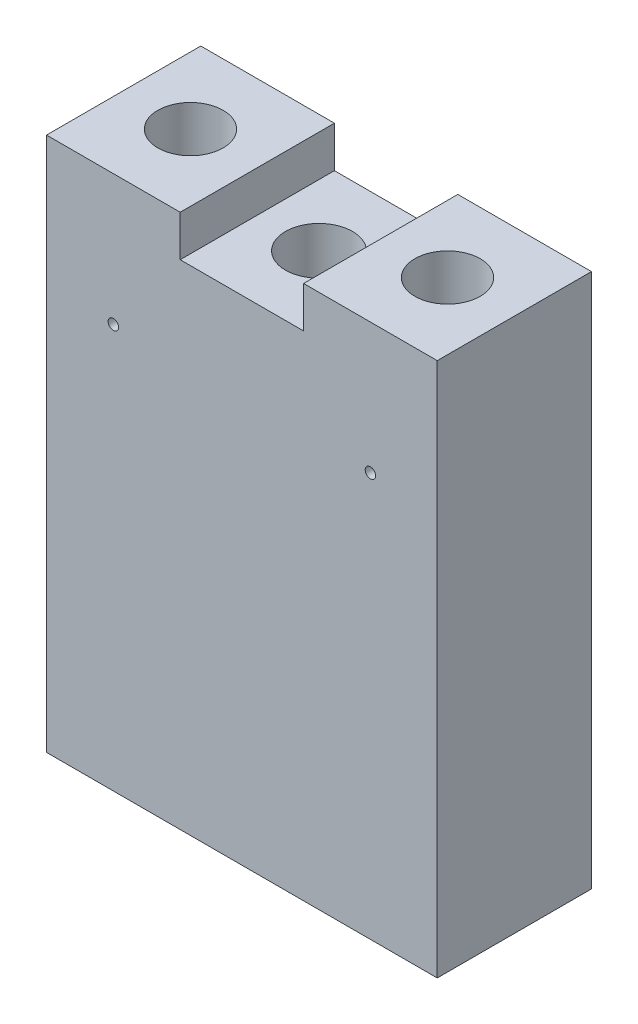
SolidWorks part; units mm, degrees
ref_plane "Front" through (0, 0, 0) normal (0, 0, 1) x (1, 0, 0)
ref_plane "Top" through (0, 0, 0) normal (0, 1, 0) x (1, 0, 0)
ref_plane "Right" through (0, 0, 0) normal (1, 0, 0) x (0, 0, -1)
sketch "Sketch1" plane through (0, 0, 0) normal (0, 0, 1) x (1, 0, 0)
  line L1 (-19, 52) -> (19, 52)
  line L2 (-19, 52) -> (-19, 0)
  line L3 (-19, 0) -> (19, 0)
  line L4 (19, 52) -> (19, 0)
  dimension "D1" = 52
  dimension "D2" = 38
extrude "Extrude1" add sketch "Sketch1" along normal blind 15
sketch "Sketch3" plane through (0, 52, 0) normal (0, 1, 0) x (-1, 0, 0)
  line L0 (0, 0) -> (0, 15) construction
  line L1 (-19, 15) -> (19, 15) construction
  circle A0 centre (12.5, 7.5) radius 3.175
  circle A1 centre (-12.5, 7.5) radius 3.175
  dimension "D1" = 6.35
  dimension "D2" = 25
  dimension "D3" = 7.5
extrude "Cut-Extrude2" cut sketch "Sketch3" against normal blind 18
sketch "Sketch5" plane through (0, 52, 0) normal (0, 1, 0) x (-1, 0, 0)
  line L0 (-19, 0) -> (19, 0) construction
  line L1 (6, 0) -> (-6, 0)
  line L2 (6, 0) -> (6, 15)
  line L3 (6, 15) -> (-6, 15)
  line L4 (-6, 0) -> (-6, 15)
  line L5 (-19, 15) -> (19, 15) construction
  dimension "D1" = 12
extrude "Cut-Extrude4" cut sketch "Sketch5" against normal blind 4
hole_wizard "1/4 Clearance Hole1" positions "Sketch11" profile "Sketch10" hole size "1/4" standard "Ansi Inch" end condition through all
sketch "Sketch11" plane through (0, 48, 0) normal (0, 1, 0) x (-1, 0, 0)
  point P0 (0, 7.5)
  dimension "D1" = 7.5
sketch "Sketch10" plane through (0, 48, 7.5) normal (1, 0, 0) x (0, 0, 1)
  line L0 (0, 0) -> (0, 48)
  line L1 (0, 48) -> (3.2639, 48)
  line L2 (3.2639, 48) -> (3.2639, 0)
  line L5 (3.2639, 0) -> (0, 0)
  line L11 (0, -6.35) -> (0, 107.95) construction
  dimension "Thru Hole Dia." = 6.5278
  dimension "Thru Hole Depth" = 48
sketch "Sketch12" plane through (0, 0, 15) normal (0, 0, 1) x (1, 0, 0)
  line L0 (12.5, 34) -> (12.5, 46.5621) construction
  line L1 (15.675, 34) -> (9.325, 34) construction
  line L2 (-12.5, 34) -> (-12.5, 45.1303) construction
  line L3 (-9.325, 34) -> (-15.675, 34) construction
  line L4 (19, 52) -> (6, 52) construction
  circle A0 centre (-12.5, 39.3) radius 0.508
  circle A1 centre (12.5, 39.3) radius 0.508
  dimension "D1" = 1.016
  dimension "D2" = 12.7
extrude "Cut-Extrude5" cut sketch "Sketch12" against normal up to next
